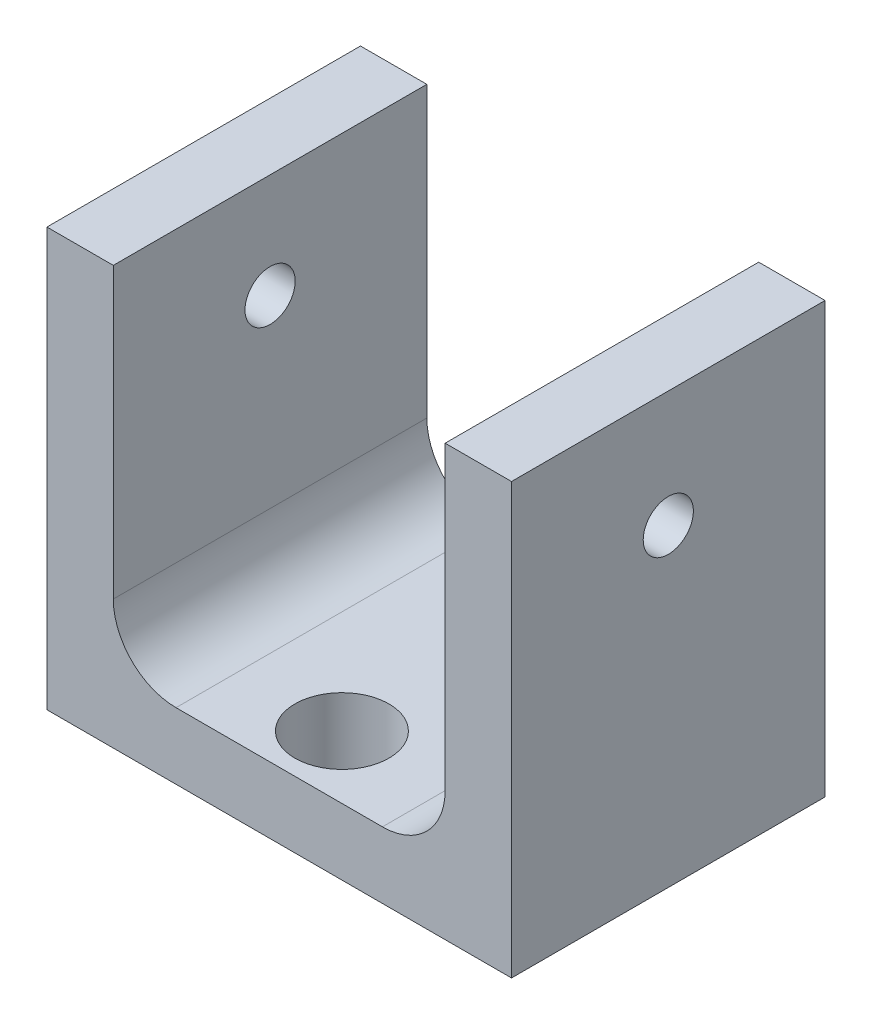
SolidWorks part; units mm, degrees
material "6061-T6 (SS)"
ref_plane "Front Plane" through (0, 0, 0) normal (0, 0, 1) x (1, 0, 0)
ref_plane "Top Plane" through (0, 0, 0) normal (0, 1, 0) x (1, 0, 0)
ref_plane "Right Plane" through (0, 0, 0) normal (1, 0, 0) x (0, 0, -1)
sketch "Sketch1" plane through (0, 0, 0) normal (0, 0, 1) x (1, 0, 0)
  line L0 (0, 0) -> (22.225, 0)
  line L1 (22.225, 0) -> (22.225, 20.5699)
  line L2 (22.225, 20.5699) -> (19.05, 20.5699)
  line L3 (19.05, 20.5699) -> (19.05, 6.175)
  line L4 (16.05, 3.175) -> (6.175, 3.175)
  line L5 (3.175, 6.175) -> (3.175, 20)
  line L6 (3.175, 20) -> (0, 20)
  line L7 (0, 20) -> (0, 0)
  arc A0 (19.05, 6.175) -> (16.05, 3.175) centre (16.05, 6.175) cw
  arc A1 (6.175, 3.175) -> (3.175, 6.175) centre (6.175, 6.175) cw
  dimension "D5" = 3
  dimension "D1" = 22.225
  dimension "D2" = 3.175
  dimension "D3" = 3.175
  dimension "D4" = 3.175
  dimension "D6" = 20
extrude "Boss-Extrude1" add sketch "Sketch1" along normal mid plane 15
sketch "Sketch4" plane through (0, 3.175, 0) normal (0, 1, 0) x (1, 0, 0)
  line L0 (16.05, -7.5) -> (6.175, -7.5) construction
  line L1 (16.05, 7.5) -> (6.175, 7.5) construction
  point P0 (11.1125, -4.5)
  point P2 (11.1125, 4.5)
  point P6 (0, 0)
  point P9 (11.1125, -7.5)
  dimension "D1" = 3
  dimension "D2" = 3
hole_wizard "M4 Clearance Hole1" positions "Sketch4" profile "Sketch3" hole size "M4" standard "ANSI Metric" end condition through all
sketch "Sketch3" plane through (11.1125, 3.175, 4.5) normal (1, 0, 0) x (0, 0, 1)
  line L0 (0, 0) -> (0, 3.175)
  line L1 (0, 3.175) -> (2.25, 3.175)
  line L2 (2.25, 3.175) -> (2.25, 0)
  line L5 (2.25, 0) -> (0, 0)
  line L11 (0, -6.35) -> (0, 107.95) construction
  dimension "Thru Hole Dia." = 4.5
  dimension "Thru Hole Depth" = 3.175
sketch "Sketch7" plane through (0, 0, 0) normal (-1, 0, 0) x (0, 0, 1)
  line L0 (7.5, 0) -> (-7.5, 0) construction
  point P0 (0, 15)
  point P3 (0, 0)
  dimension "D1" = 15
hole_wizard "M2 Clearance Hole1" positions "Sketch7" profile "Sketch6" hole size "M2" standard "ANSI Metric" end condition through all
sketch "Sketch6" plane through (0, 15, 0) normal (0, 1, 0) x (0, 0, 1)
  line L0 (0, 0) -> (0, 22.225)
  line L1 (0, 22.225) -> (1.2, 22.225)
  line L2 (1.2, 22.225) -> (1.2, 0)
  line L5 (1.2, 0) -> (0, 0)
  line L11 (0, -6.35) -> (0, 107.95) construction
  dimension "Thru Hole Dia." = 2.4
  dimension "Thru Hole Depth" = 22.225
